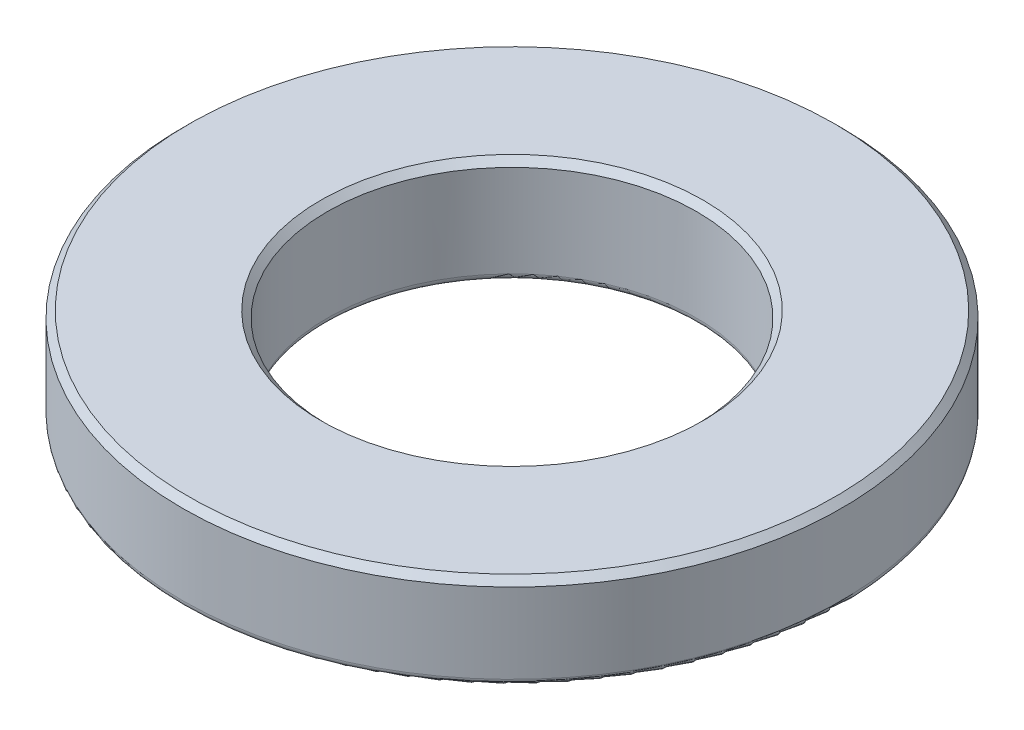
SolidWorks part; units mm, degrees
material "304 SSTL"
ref_plane "Front" through (0, 0, 0) normal (0, 0, 1) x (1, 0, 0)
ref_plane "Top" through (0, 0, 0) normal (0, 1, 0) x (1, 0, 0)
ref_plane "Right" through (0, 0, 0) normal (1, 0, 0) x (0, 0, -1)
sketch "Sketch1" plane through (0, 0, 0) normal (0, 0, 1) x (1, 0, 0)
  line L0 (0, 0) -> (0, -106.68) construction
  line L2 (6.858, -110.2693) -> (12.7, -110.2693)
  line L3 (12.7, -110.2693) -> (12.7, -105.9214)
  line L6 (6.858, -106.4593) -> (6.858, -110.2693)
  arc A0 (6.858, -106.4593) -> (12.7, -105.9214) centre (0, 0) ccw construction
  arc A1 (6.858, -106.4593) -> (12.7, -105.9214) centre (0, 0) ccw
  circle A2 centre (0, 0) radius 106.68 construction
  dimension "D1" = 213.36
  dimension "D2" = 6.858
  dimension "D3" = 12.7
  dimension "D4" = 3.81
sketch "Sketch2" plane through (0, 0, 0) normal (0, 0, 1) x (1, 0, 0)
  line L0 (12.7, -110.2693) -> (12.7, -105.9214) construction
  line L2 (12.7, -102.362) -> (12.7, -105.9214)
  line L3 (7.112, -106.4427) -> (7.112, -102.362)
  line L4 (7.112, -102.362) -> (12.7, -102.362)
  line L5 (0, 0) -> (0, -106.68) construction
  arc A0 (6.858, -106.4593) -> (12.7, -105.9214) centre (0, 0) ccw construction
  arc A1 (7.112, -106.4427) -> (12.7, -105.9214) centre (0, 0) ccw
  circle A2 centre (0, 0) radius 106.68 construction
  dimension "D2" = 5.588
  dimension "D1" = 4.318
revolve "Convex Revolve1" add sketch "Sketch2" angle 360 about L5
chamfer "Chamfer1" distance 0.254 angle 45 2 edges at (0, -102.362, 7.112) (0, -102.362, 12.7)
fillet "Fillet4" radius 0.254 2 edges at (0, -105.9214, 12.7) (0, -106.4427, 7.112)
